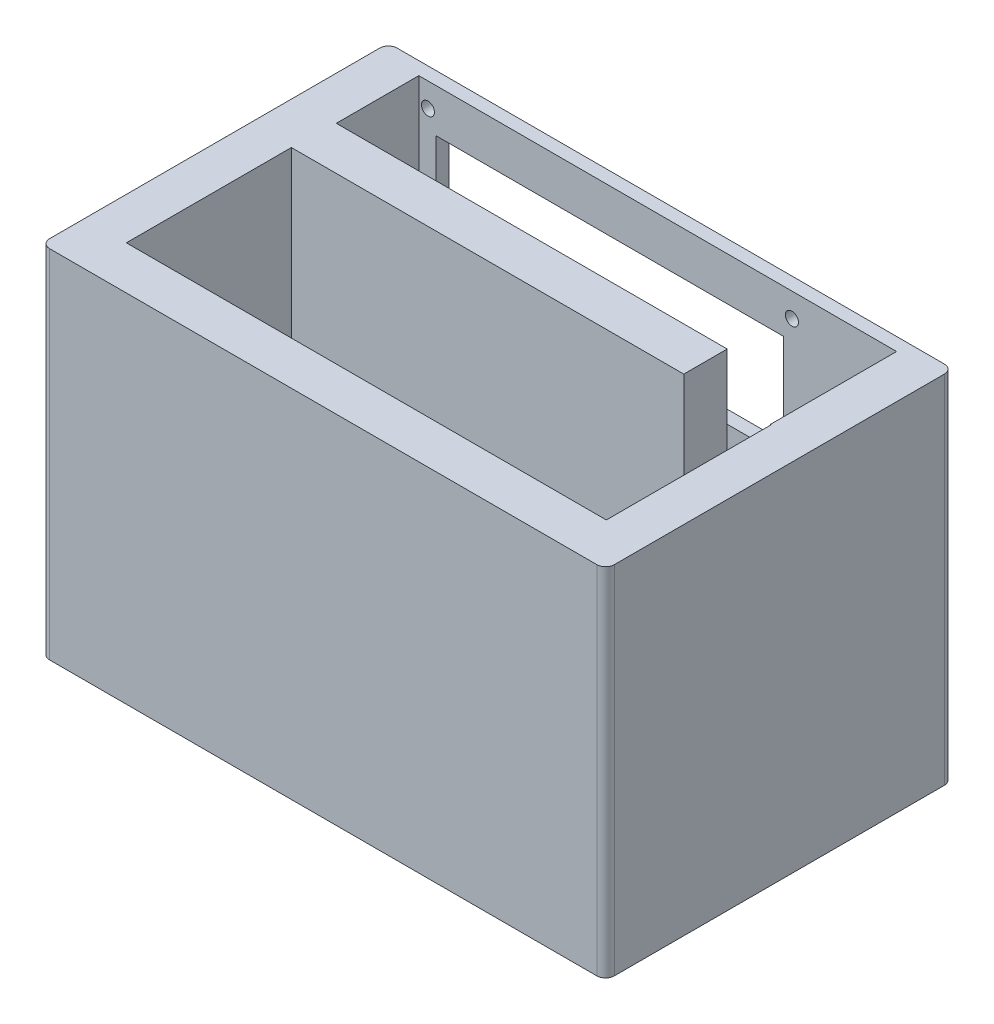
SolidWorks part; units mm, degrees
ref_plane "Plan de face" through (0, 0, 0) normal (0, 0, 1) x (1, 0, 0)
ref_plane "Plan de dessus" through (0, 0, 0) normal (0, 1, 0) x (1, 0, 0)
ref_plane "Plan de droite" through (0, 0, 0) normal (1, 0, 0) x (0, 0, -1)
sketch "Esquisse1" plane through (0, 0, 0) normal (0, 1, 0) x (1, 0, 0)
  line L1 (-65, 40) -> (65, 40)
  line L2 (-65, 40) -> (-65, -40)
  line L3 (-65, -40) -> (65, -40)
  line L4 (65, 40) -> (65, -40)
  point P4 (0, -40)
  dimension "D1" = 65
  dimension "D2" = 130
  dimension "D3" = 80
  dimension "D4" = 40
extrude "Boss.-Extru.1" add sketch "Esquisse1" along normal blind 82
sketch "Esquisse4" plane through (0, 82, 0) normal (0, 1, 0) x (1, 0, 0)
  line L0 (65, -40) -> (65, 40) construction
  line L1 (55, 18) -> (-55, 18)
  line L2 (55, 18) -> (55, 37)
  line L3 (55, 37) -> (-55, 37)
  line L4 (-55, 18) -> (-55, 37)
  line L5 (65, 40) -> (-65, 40) construction
  line L6 (-65, 40) -> (-65, -40) construction
  dimension "D1" = 10
  dimension "D2" = 3
  dimension "D3" = 10
  dimension "D4" = 19
extrude "Enlèv. mat.-Extru.1" cut sketch "Esquisse4" against normal blind 77
sketch "Esquisse7" plane through (0, 0, -40) normal (0, 0, -1) x (-1, 0, 0)
  line L0 (65, 82) -> (65, 0) construction
  line L1 (-29, 35) -> (51, 35)
  line L2 (-29, 35) -> (-29, 11)
  line L3 (-29, 11) -> (51, 11)
  line L4 (51, 35) -> (51, 11)
  line L5 (-65, 0) -> (65, 0) construction
  dimension "D1" = 14
  dimension "D2" = 11
  dimension "D3" = 80
  dimension "D4" = 24
extrude "Enlèv. mat.-Extru.2" cut sketch "Esquisse7" against normal blind 5
sketch "Esquisse8" plane through (0, 0, -40) normal (0, 0, -1) x (-1, 0, 0)
  line L0 (51, 35) -> (-29, 35) construction
  line L1 (-29, 72) -> (51, 72)
  line L2 (-29, 72) -> (-29, 48)
  line L3 (-29, 48) -> (51, 48)
  line L4 (51, 72) -> (51, 48)
  line L7 (65, 82) -> (65, 0) construction
  dimension "D1" = 13
  dimension "D2" = 24
  dimension "D3" = 80
  dimension "D4" = 14
extrude "Enlèv. mat.-Extru.3" cut sketch "Esquisse8" against normal blind 5
fillet "Congé1" radius 2 4 edges at (65, 41, 40) (-65, 41, 40) (-65, 41, -40) (65, 41, -40)
sketch "Esquisse9" plane through (0, 82, 0) normal (0, 1, 0) x (1, 0, 0)
  line L0 (-63, -40) -> (63, -40) construction
  line L1 (-55.3379, -30) -> (55.1719, -30)
  line L2 (-55.3379, -30) -> (-55.3379, 8)
  line L3 (-55.3379, 8) -> (55.1719, 8)
  line L4 (55.1719, -30) -> (55.1719, 8)
  line L5 (-55, 18) -> (55, 18) construction
  dimension "D1" = 10
  dimension "D2" = 10
extrude "Enlèv. mat.-Extru.4" cut sketch "Esquisse9" against normal blind 77
sketch "Esquisse10" plane through (0, 82, 0) normal (0, 1, 0) x (1, 0, 0)
  line L0 (55, 18) -> (55, 37) construction
  line L1 (35, 8) -> (55, 8)
  line L2 (35, 8) -> (35, 18)
  line L3 (35, 18) -> (55, 18)
  line L4 (55, 8) -> (55, 18)
  line L5 (55.1719, 8) -> (-55.3379, 8) construction
  line L6 (-55, 18) -> (55, 18) construction
  dimension "D1" = 0
  dimension "D2" = 20
  dimension "D3" = 0
  dimension "D4" = 0
extrude "Enlèv. mat.-Extru.5" cut sketch "Esquisse10" against normal blind 77
sketch "Esquisse11" plane through (0, 0, -40) normal (0, 0, -1) x (-1, 0, 0)
  line L0 (51, 35) -> (-29, 35) construction
  line L2 (-29, 35) -> (-29, 11) construction
  circle A0 centre (-30.9, 39.5) radius 1.5
  point P6 (-29, 31.8582)
  dimension "D1" = 3
  dimension "D2" = 4.5
  dimension "D3" = 1.9
extrude "Enlèv. mat.-Extru.6" cut sketch "Esquisse11" against normal up to next (3 mm away)
ref_plane "Plan1" through (-11, 0, 0) normal (1, 0, 0) x (0, 0, -1)
sketch "Esquisse12" plane through (0, 0, -40) normal (0, 0, -1) x (-1, 0, 0)
  line L1 (-29, 72) -> (-29, 48) construction
  line L2 (-29, 48) -> (51, 48) construction
  circle A0 centre (-30.9, 45.5) radius 1.5
  dimension "D1" = 3
  dimension "D2" = 1.9
  dimension "D3" = 2.5
extrude "Enlèv. mat.-Extru.7" cut sketch "Esquisse12" against normal up to next (3 mm away)
mirror "Symétrie1" about plane through (-11, 0, 0) normal (1, 0, 0) of "Enlèv. mat.-Extru.6", "Enlèv. mat.-Extru.7"
sketch "Esquisse13" plane through (0, 0, -40) normal (0, 0, -1) x (-1, 0, 0)
  line L0 (51, 72) -> (-29, 72) construction
  line L2 (-29, 72) -> (-29, 48) construction
  circle A0 centre (-30.9, 76.5) radius 1.5
  point P6 (-29, 69.0132)
  dimension "D1" = 3
  dimension "D2" = 4.5
  dimension "D3" = 1.9
extrude "Enlèv. mat.-Extru.8" cut sketch "Esquisse13" against normal up to next (3 mm away)
mirror "Symétrie2" about plane through (-11, 0, 0) normal (1, 0, 0) of "Enlèv. mat.-Extru.8"
sketch "Esquisse14" plane through (0, 0, -40) normal (0, 0, -1) x (-1, 0, 0)
  line L0 (-29, 35) -> (-29, 11) construction
  line L1 (-29, 11) -> (51, 11) construction
  circle A0 centre (-30.9, 8.5) radius 1.5
  point P6 (-78.3876, 98.3771)
  dimension "D1" = 3
  dimension "D2" = 1.9
  dimension "D3" = 2.5
extrude "Enlèv. mat.-Extru.11" cut sketch "Esquisse14" against normal up to next (3 mm away)
mirror "Symétrie3" about plane through (-11, 0, 0) normal (1, 0, 0) of "Enlèv. mat.-Extru.11"
